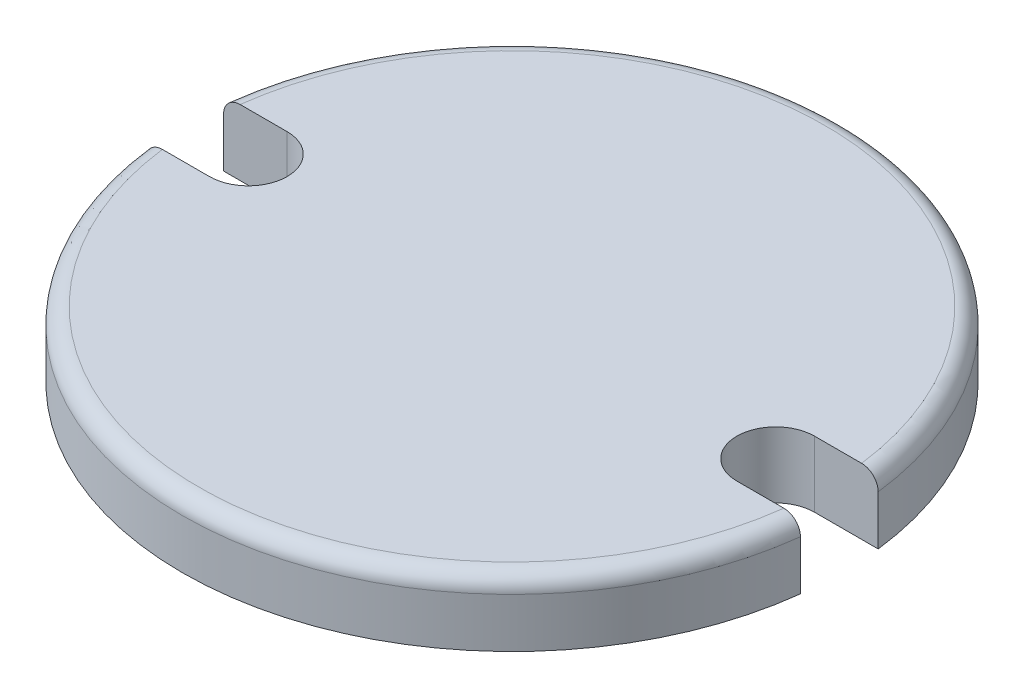
SolidWorks part; units mm, degrees
ref_plane "Front Plane" through (0, 0, 0) normal (0, 0, 1) x (1, 0, 0)
ref_plane "Top Plane" through (0, 0, 0) normal (0, 1, 0) x (1, 0, 0)
ref_plane "Right Plane" through (0, 0, 0) normal (1, 0, 0) x (0, 0, -1)
sketch "Sketch1" plane through (0, 0, 0) normal (0, 1, 0) x (1, 0, 0)
  circle A1 centre (0, 0) radius 63.5
extrude "Boss-Extrude2" add sketch "Sketch1" along normal blind 12.7
fillet "Fillet2" radius 3.17 1 edges at (0, 12.7, 63.5)
sketch "Sketch3" plane through (0, 12.7, 0) normal (0, 1, 0) x (1, 0, 0)
  line L0 (0, 60.33) -> (0, -60.33) construction
  line L1 (-50.8, 7.49) -> (-63.0567, 7.49)
  line L2 (-50.8, -7.49) -> (-63.0567, -7.49)
  line L3 (50.8, -7.49) -> (63.0567, -7.49)
  line L4 (50.8, 7.49) -> (63.0567, 7.49)
  arc A0 (-50.8, -7.49) -> (-50.8, 7.49) centre (-50.8, 0) ccw
  arc A1 (50.8, 7.49) -> (50.8, -7.49) centre (50.8, 0) ccw
  circle A2 centre (0, 0) radius 60.33 construction
  circle A3 centre (0, 0) radius 63.5 construction
  arc A4 (-63.0567, 7.49) -> (-63.0567, -7.49) centre (0, 0) ccw
  arc A5 (63.0567, -7.49) -> (63.0567, 7.49) centre (0, 0) ccw
  dimension "D1" = 14.98
  dimension "D2" = 14.98
  dimension "D3" = 101.6
extrude "Cut-Extrude1" cut sketch "Sketch3" against normal through all contours L1 A4 L2 A0 | L4 A5 L3 A1
sketch "Sketch5" plane through (0, 0, 0) normal (0, 1, 0) x (1, 0, 0)
  line L1 (31.75, -34.92) -> (-31.75, -34.92)
  line L2 (-31.75, 0) -> (-31.75, -34.92)
  line L3 (31.75, 0) -> (31.75, -34.92)
  line L5 (31.75, -34.92) -> (-31.75, -34.92)
  arc A0 (31.75, 0) -> (-31.75, 0) centre (0, 0) ccw
  point P0 (50.8, 0)
  point P1 (-50.8, 0)
  point P3 (50.8, -34.92)
  point P4 (-50.8, -34.92)
